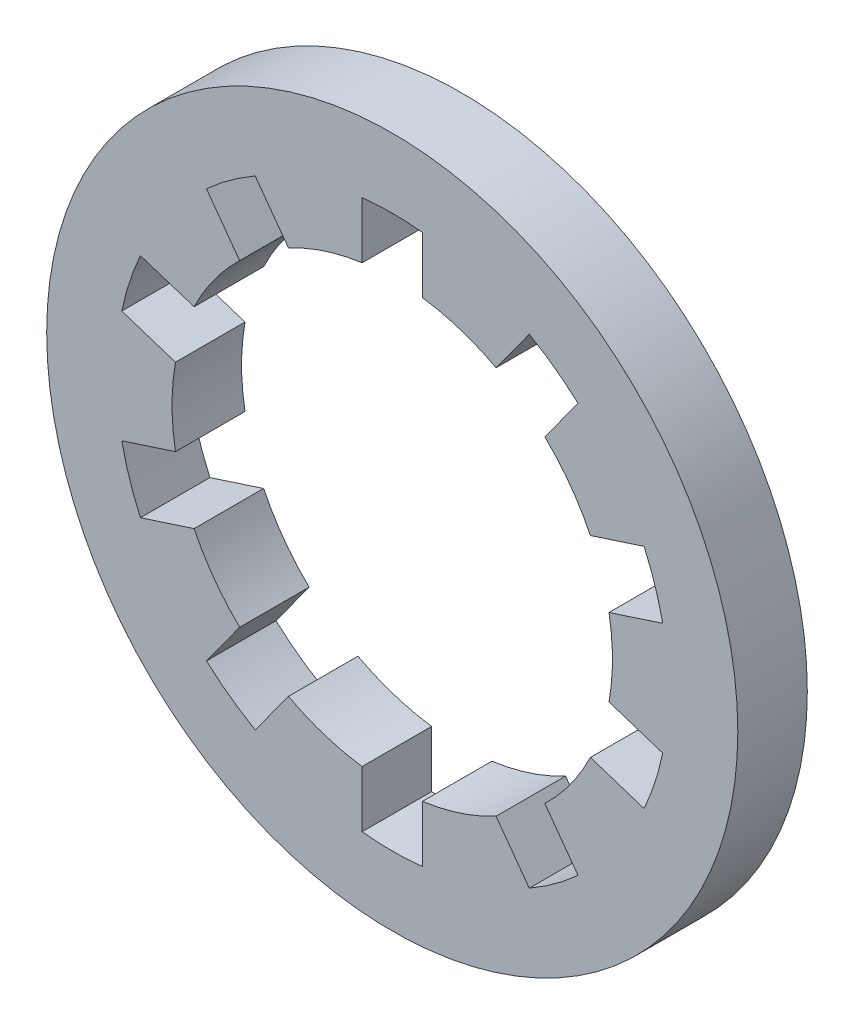
SolidWorks part; units mm, degrees
material "Stop odlewniczy stali"
ref_plane "Płaszczyzna przednia" through (0, 0, 0) normal (0, 0, 1) x (1, 0, 0)
ref_plane "Płaszczyzna górna" through (0, 0, 0) normal (0, 1, 0) x (1, 0, 0)
ref_plane "Płaszczyzna prawa" through (0, 0, 0) normal (1, 0, 0) x (0, 0, -1)
sketch "Szkic1" plane through (0, 0, 0) normal (0, 0, 1) x (1, 0, 0)
  circle A0 centre (0, 0) radius 8.6
extrude "Dodanie-wyciągnięcie1" add sketch "Szkic1" along normal blind 1.73 contours A0
sketch "Szkic2" plane through (0, 0, 1.73) normal (0, 0, 1) x (1, 0, 0)
  line L22 (-2.584, 4.8325) -> (-3.4101, 5.9696)
  line L23 (-0.75, 5.4284) -> (-0.75, 6.834)
  line L24 (0.75, 5.4284) -> (0.75, 6.834)
  line L25 (2.584, 4.8325) -> (3.4101, 5.9696)
  line L26 (3.7975, 3.9509) -> (4.6237, 5.088)
  line L27 (4.931, 2.3908) -> (6.2677, 2.8251)
  line L28 (5.3945, 0.9642) -> (6.7313, 1.3985)
  line L29 (5.3945, -0.9642) -> (6.7313, -1.3985)
  line L30 (4.931, -2.3908) -> (6.2677, -2.8251)
  line L31 (3.7975, -3.9509) -> (4.6237, -5.088)
  line L32 (2.584, -4.8325) -> (3.4101, -5.9696)
  line L33 (0.75, -5.4284) -> (0.75, -6.834)
  line L34 (-0.75, -5.4284) -> (-0.75, -6.834)
  line L35 (-2.584, -4.8325) -> (-3.4101, -5.9696)
  line L36 (-3.7975, -3.9509) -> (-4.6237, -5.088)
  line L37 (-4.931, -2.3908) -> (-6.2677, -2.8251)
  line L38 (-5.3945, -0.9642) -> (-6.7313, -1.3985)
  line L39 (-5.3945, 0.9642) -> (-6.7313, 1.3985)
  line L40 (-4.931, 2.3908) -> (-6.2677, 2.8251)
  line L41 (-3.7975, 3.9509) -> (-4.6237, 5.088)
  arc A0 (-3.7975, 3.9509) -> (-4.931, 2.3908) centre (0, 0) ccw
  arc A1 (-3.4101, 5.9696) -> (-4.6237, 5.088) centre (0, 0) ccw
  arc A3 (0.75, 6.834) -> (-0.75, 6.834) centre (0, 0) ccw
  arc A4 (4.6237, 5.088) -> (3.4101, 5.9696) centre (0, 0) ccw
  arc A5 (6.7313, 1.3985) -> (6.2677, 2.8251) centre (0, 0) ccw
  arc A6 (6.2677, -2.8251) -> (6.7313, -1.3985) centre (0, 0) ccw
  arc A7 (3.4101, -5.9696) -> (4.6237, -5.088) centre (0, 0) ccw
  arc A8 (-0.75, -6.834) -> (0.75, -6.834) centre (0, 0) ccw
  arc A9 (-4.6237, -5.088) -> (-3.4101, -5.9696) centre (0, 0) ccw
  arc A10 (-6.7313, -1.3985) -> (-6.2677, -2.8251) centre (0, 0) ccw
  arc A11 (-6.2677, 2.8251) -> (-6.7313, 1.3985) centre (0, 0) ccw
  arc A12 (-0.75, 5.4284) -> (-2.584, 4.8325) centre (0, 0) ccw
  arc A13 (2.584, 4.8325) -> (0.75, 5.4284) centre (0, 0) ccw
  arc A14 (4.931, 2.3908) -> (3.7975, 3.9509) centre (0, 0) ccw
  arc A15 (5.3945, -0.9642) -> (5.3945, 0.9642) centre (0, 0) ccw
  arc A16 (3.7975, -3.9509) -> (4.931, -2.3908) centre (0, 0) ccw
  arc A17 (0.75, -5.4284) -> (2.584, -4.8325) centre (0, 0) ccw
  arc A18 (-2.584, -4.8325) -> (-0.75, -5.4284) centre (0, 0) ccw
  arc A19 (-4.931, -2.3908) -> (-3.7975, -3.9509) centre (0, 0) ccw
  arc A20 (-5.3945, 0.9642) -> (-5.3945, -0.9642) centre (0, 0) ccw
extrude "Wytnij-wyciągnięcie1" cut sketch "Szkic2" against normal up to surface (1.73 mm away) up to face at (8.6, 0, 0)
